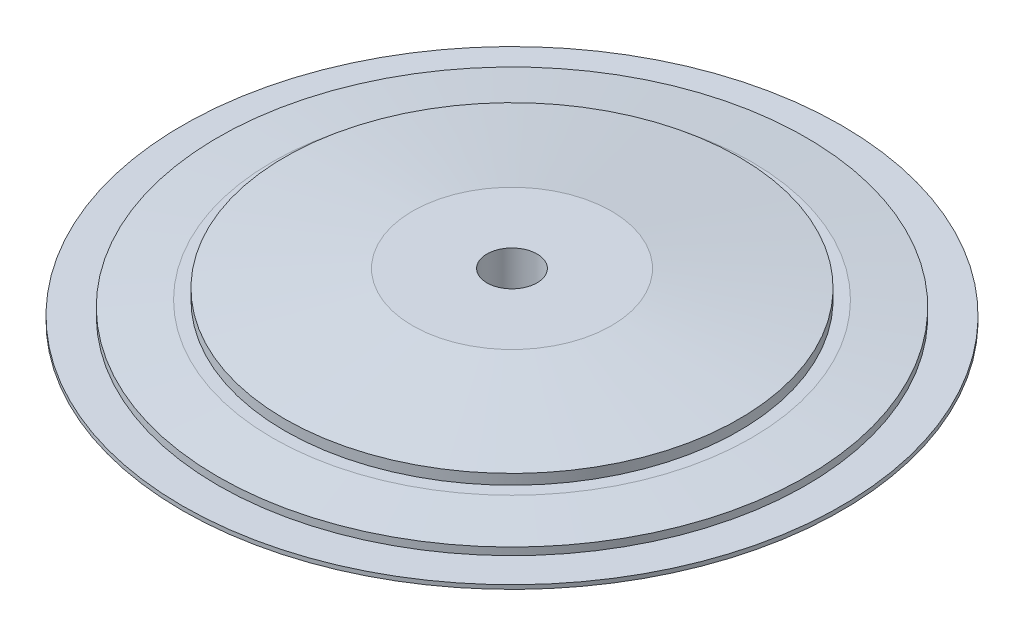
SolidWorks part; units mm, degrees
ref_plane "Front" through (0, 0, 0) normal (0, 0, 1) x (1, 0, 0)
ref_plane "Top" through (0, 0, 0) normal (0, 1, 0) x (1, 0, 0)
ref_plane "Right" through (0, 0, 0) normal (1, 0, 0) x (0, 0, -1)
sketch "Sketch1" plane through (0, 0, 0) normal (0, 0, 1) x (1, 0, 0)
  line L0 (7.9882, 0) -> (105.038, 0)
  line L1 (105.038, 0) -> (105.038, 1.3004)
  line L2 (105.038, 1.3004) -> (93.7001, 1.3004)
  line L3 (93.7001, 1.3004) -> (93.7001, 3.6783)
  line L4 (76.2837, 5.654) -> (72.3679, 5.654)
  line L5 (72.3679, 5.654) -> (72.3679, 8.9199)
  line L6 (31.6762, 14.3376) -> (7.9882, 14.3376)
  line L7 (0, 11.676) -> (0, 0) construction
  line L8 (7.9882, 14.3376) -> (7.9882, 0)
  line L9 (72.3679, 8.9199) -> (31.6762, 14.3376)
  line L10 (93.7001, 3.6783) -> (76.2837, 5.654)
revolve "Revolve1" add sketch "Sketch1" angle 360 about L7
